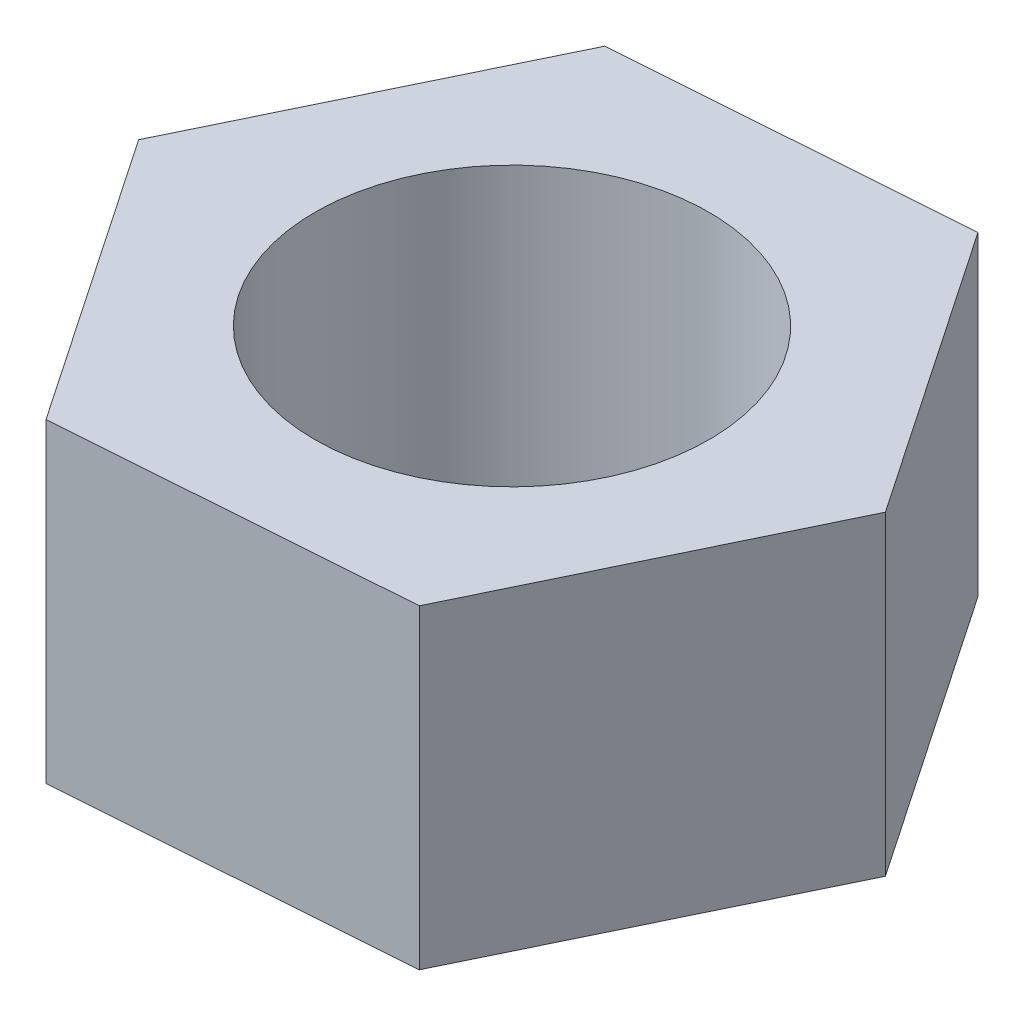
SolidWorks part; units mm, degrees
ref_plane "Front Plane" through (0, 0, 0) normal (0, 0, 1) x (1, 0, 0)
ref_plane "Top Plane" through (0, 0, 0) normal (0, 1, 0) x (1, 0, 0)
ref_plane "Right Plane" through (0, 0, 0) normal (1, 0, 0) x (0, 0, -1)
sketch "Sketch1" plane through (0, 0, 0) normal (0, 1, 0) x (1, 0, 0)
  line L1 (14.921, -21.9703) -> (26.4874, 1.9368)
  line L2 (26.4874, 1.9368) -> (11.5664, 23.9072)
  line L3 (11.5664, 23.9072) -> (-14.921, 21.9703)
  line L4 (-14.921, 21.9703) -> (-26.4874, -1.9368)
  line L5 (-26.4874, -1.9368) -> (-11.5664, -23.9072)
  line L6 (-11.5664, -23.9072) -> (14.921, -21.9703)
  circle A0 centre (0, 0) radius 23 construction
  dimension "D1" = 46
extrude "Boss-Extrude1" add sketch "Sketch1" along normal blind 24
sketch "Sketch2" plane through (0, 24, 0) normal (0, 1, 0) x (1, 0, 0)
  circle A0 centre (0, 0) radius 15
extrude "Cut-Extrude1" cut sketch "Sketch2" against normal through all
